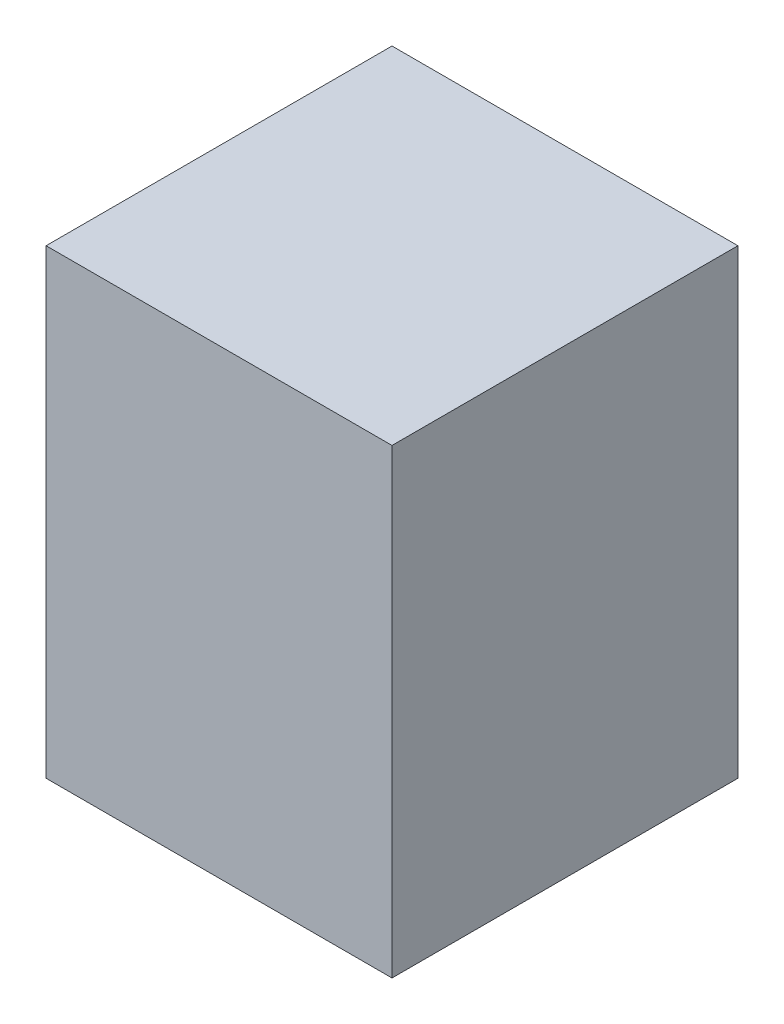
SolidWorks part; units mm, degrees
ref_plane "Front Plane" through (0, 0, 0) normal (0, 0, 1) x (1, 0, 0)
ref_plane "Top Plane" through (0, 0, 0) normal (0, 1, 0) x (1, 0, 0)
ref_plane "Right Plane" through (0, 0, 0) normal (1, 0, 0) x (0, 0, -1)
sketch "Sketch1" plane through (0, 0, 0) normal (0, 1, 0) x (1, 0, 0)
  line L1 (0, 0) -> (304.8, 0)
  line L2 (0, 0) -> (0, 304.8)
  line L3 (0, 304.8) -> (304.8, 304.8)
  line L4 (304.8, 0) -> (304.8, 304.8)
  dimension "D1" = 304.8
  dimension "D2" = 304.8
extrude "Boss-Extrude1" add sketch "Sketch1" along normal blind 406.4
